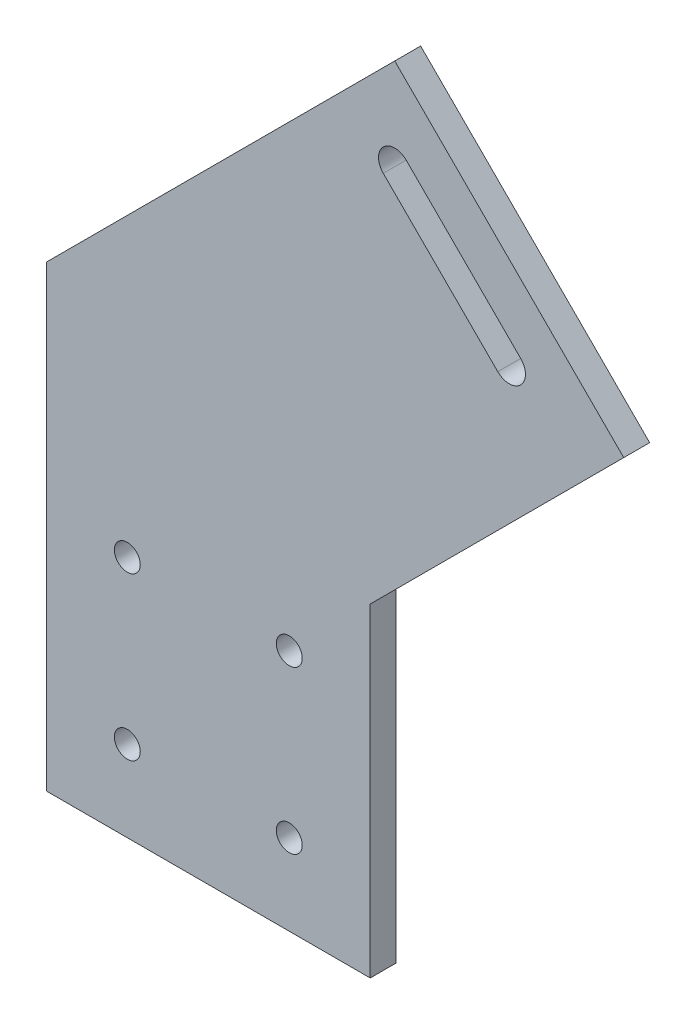
SolidWorks part; units mm, degrees
ref_plane "Front Plane" through (0, 0, 0) normal (0, 0, 1) x (1, 0, 0)
ref_plane "Top Plane" through (0, 0, 0) normal (0, 1, 0) x (1, 0, 0)
ref_plane "Right Plane" through (0, 0, 0) normal (1, 0, 0) x (0, 0, -1)
sketch "Sketch1" plane through (0, 0, 0) normal (0, 0, 1) x (1, 0, 0)
  line L0 (28.7833, 114.494) -> (64.1386, 79.1386)
  line L2 (25, -10) -> (25, 40)
  line L4 (-25, -10) -> (-25, 40)
  line L5 (6.25, -10) -> (-25, 40) construction
  line L6 (25, 40) -> (-6.25, -10) construction
  line L11 (12.5, 2.5) -> (-12.5, 27.5) construction
  line L12 (12.5, 27.5) -> (-12.5, 2.5) construction
  line L13 (28.7833, 114.494) -> (-25, 60.7107)
  line L14 (25, 40) -> (64.1386, 79.1386)
  line L15 (-25, 40) -> (-25, 60.7107)
  line L16 (-25, -10) -> (25, -10)
  line L17 (48.2287, 84.4419) -> (30.551, 102.1196)
  line L18 (27.0155, 98.5841) -> (44.6932, 80.9064)
  circle A1 centre (-12.5, 27.5) radius 2
  circle A5 centre (12.5, 27.5) radius 2
  circle A6 centre (12.5, 2.5) radius 2
  circle A7 centre (-12.5, 2.5) radius 2
  arc A8 (30.551, 102.1196) -> (27.0155, 98.5841) centre (28.7833, 100.3518) ccw
  arc A9 (44.6932, 80.9064) -> (48.2287, 84.4419) centre (46.4609, 82.6742) ccw
  point P0 (0, 0)
  point P8 (0, 15)
  point P23 (0, 11.0497)
  dimension "D6" = 4
  dimension "D10" = 25
  dimension "D7" = 5
  dimension "D9" = 5
  dimension "D2" = 50
  dimension "D3" = 15
  dimension "D4" = 25
  dimension "D5" = 50
  dimension "D8" = 50
  dimension "D11" = 10
  dimension "D12" = 10
extrude "Boss-Extrude1" add sketch "Sketch1" along normal blind 4
